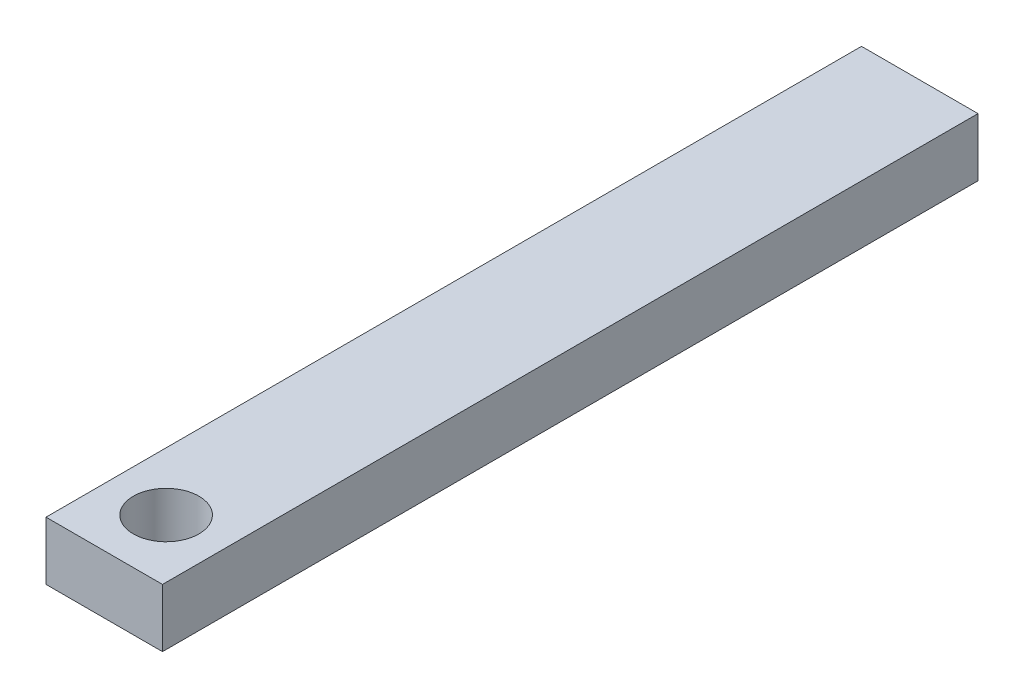
SolidWorks part; units mm, degrees
ref_plane "Front Plane" through (0, 0, 0) normal (0, 0, 1) x (1, 0, 0)
ref_plane "Top Plane" through (0, 0, 0) normal (0, 1, 0) x (1, 0, 0)
ref_plane "Right Plane" through (0, 0, 0) normal (1, 0, 0) x (0, 0, -1)
sketch "Sketch1" plane through (0, 0, 0) normal (0, 0, 1) x (1, 0, 0)
  line L1 (0, 0) -> (50.8, 0)
  line L2 (0, 0) -> (0, 25.4)
  line L3 (0, 25.4) -> (50.8, 25.4)
  line L4 (50.8, 0) -> (50.8, 25.4)
  dimension "D1" = 25.4
  dimension "D2" = 50.8
extrude "Boss-Extrude1" add sketch "Sketch1" along normal blind 355.6
sketch "Sketch2" plane through (0, 25.4, 0) normal (0, 1, 0) x (1, 0, 0)
  line L0 (0, -355.6) -> (0, 0) construction
  line L2 (50.8, -355.6) -> (0, -355.6) construction
  circle A0 centre (25.4, -328.6125) radius 14.2875
  point P6 (30.4816, -502.1069)
  dimension "D2" = 28.575
  dimension "D3" = 26.9875
  dimension "D1" = 25.4
extrude "Cut-Extrude1" cut sketch "Sketch2" against normal through all
